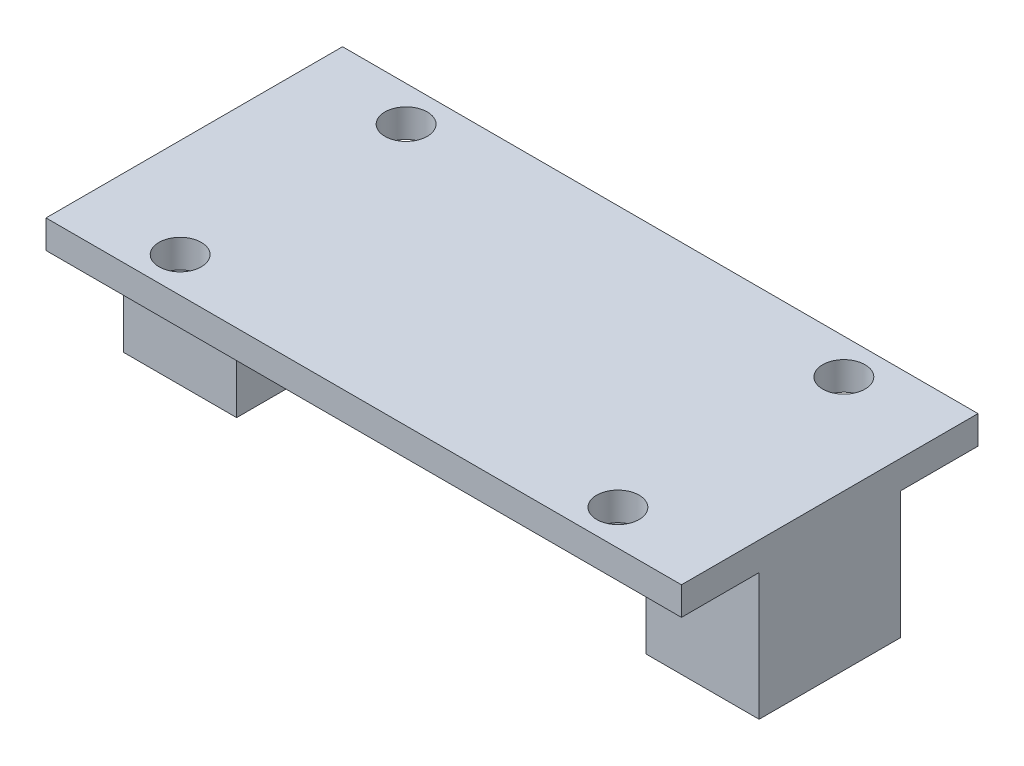
SolidWorks part; units mm, degrees
ref_plane "Płaszczyzna przednia" through (0, 0, 0) normal (0, 0, 1) x (1, 0, 0)
ref_plane "Płaszczyzna górna" through (0, 0, 0) normal (0, 1, 0) x (1, 0, 0)
ref_plane "Płaszczyzna prawa" through (0, 0, 0) normal (1, 0, 0) x (0, 0, -1)
sketch "Sketch2" plane through (0, 0, 0) normal (0, 0, 1) x (1, 0, 0)
  line L0 (0, 0) -> (17.5, 0) construction
  line L5 (0, 0) -> (-17.5, 0) construction
  line L7 (-17.5, 0) -> (-17.5, -1) construction
  line L8 (17.5, 0) -> (17.5, -1) construction
  line L9 (17.5, -1) -> (13.5, -1) construction
  line L10 (13.5, -1) -> (13.5, -7.5) construction
  line L11 (-17.5, -1) -> (-13.5, -1) construction
  line L12 (-13.5, -1) -> (-13.5, -7.5) construction
  line L13 (-13.5, -7.5) -> (13.5, -7.5) construction
  line L14 (-17.5, 0) -> (-17.5, -1) construction
  line L15 (-17.5, 0) -> (-17.5, -1)
  line L16 (-17.5, -1) -> (-14.5, -1)
  line L17 (-14.5, -1) -> (-14.5, -5)
  line L18 (-14.5, -5) -> (-22.5, -5)
  line L19 (-22.5, -5) -> (-22.5, 0)
  line L20 (-22.5, 0) -> (-22.5, 4)
  line L21 (-22.5, 4) -> (22.5, 4)
  line L22 (22.5, 4) -> (22.5, -5)
  line L23 (22.5, -5) -> (14.5, -5)
  line L24 (14.5, -5) -> (14.5, -1)
  line L25 (14.5, -1) -> (17.5, -1)
  line L26 (17.5, -1) -> (17.5, 0)
  line L27 (17.5, 0) -> (-17.5, 0)
  point P10 (-22.5, 0)
  point P11 (-22.5, -5)
  point P12 (-14.5, -5)
  point P13 (-22.5, 0)
  point P14 (-22.5, 4)
  point P16 (-14.5, -1)
  point P17 (-17.5, -1)
  point P18 (-17.5, 0)
  dimension "D1" = 5
  dimension "D2" = 5
  dimension "D3" = 8
  dimension "D4" = 4
  dimension "D5" = 0
  dimension "D6" = 0
  dimension "D7" = 35
  dimension "D8" = 1
  dimension "D9" = 4
  dimension "D10" = 4
  dimension "D11" = 1
  dimension "D12" = 27
  dimension "D13" = 6.5
  dimension "D14" = 6.5
  dimension "D16" = 3
  dimension "D17" = 1
  dimension "D18" = 9
  dimension "D19" = 9
  dimension "D20" = 8
  dimension "D21" = 1
  dimension "D22" = 0
  dimension "D23" = 0
  dimension "D25" = 45
extrude "Boss-Extrude1" add sketch "Sketch2" along normal blind 10
sketch "Sketch3" plane through (0, 4, 0) normal (0, 1, 0) x (1, 0, 0)
  line L0 (-22.5, -15.5) -> (22.5, -15.5)
  line L1 (-22.5, -15.5) -> (-22.5, 5.5)
  line L2 (-22.5, 5.5) -> (22.5, 5.5)
  line L3 (22.5, -15.5) -> (22.5, 5.5)
  line L4 (-22.5, -15.5) -> (22.5, 5.5) construction
  line L5 (-22.5, 5.5) -> (22.5, -15.5) construction
  line L6 (-22.5, -10) -> (-22.5, 0) construction
  point P0 (0, -5)
  point P1 (0, -5)
  point P6 (0, 0)
  point P10 (0, 0)
  dimension "D1" = 45
  dimension "D2" = 21
  dimension "D3" = 5
  dimension "D4" = 22.5
extrude "Boss-Extrude2" add sketch "Sketch3" along normal blind 2
sketch "Sketch4" plane through (0, 6, 0) normal (0, 1, 0) x (1, 0, 0)
  line L6 (22.5, 5.5) -> (-22.5, 5.5) construction
  line L7 (-15.5, 3) -> (15.5, 3) construction
  line L8 (-15.5, 3) -> (-15.5, -13) construction
  line L9 (-15.5, -13) -> (15.5, -13) construction
  line L10 (15.5, 3) -> (15.5, -13) construction
  line L11 (-15.5, 3) -> (15.5, -13) construction
  line L12 (-15.5, -13) -> (15.5, 3) construction
  line L13 (-22.5, 5.5) -> (-22.5, -15.5) construction
  circle A4 centre (-15.5, -13) radius 1.5
  circle A5 centre (-15.5, 3) radius 1.5
  circle A6 centre (15.5, 3) radius 1.5
  circle A7 centre (15.5, -13) radius 1.5
  point P9 (0, -5)
  point P10 (0, -5)
  dimension "D4" = 16
  dimension "D5" = 10.5
  dimension "D6" = 22.5
  dimension "D7" = 31
extrude "Cut-Extrude1" cut sketch "Sketch4" against normal blind 5
